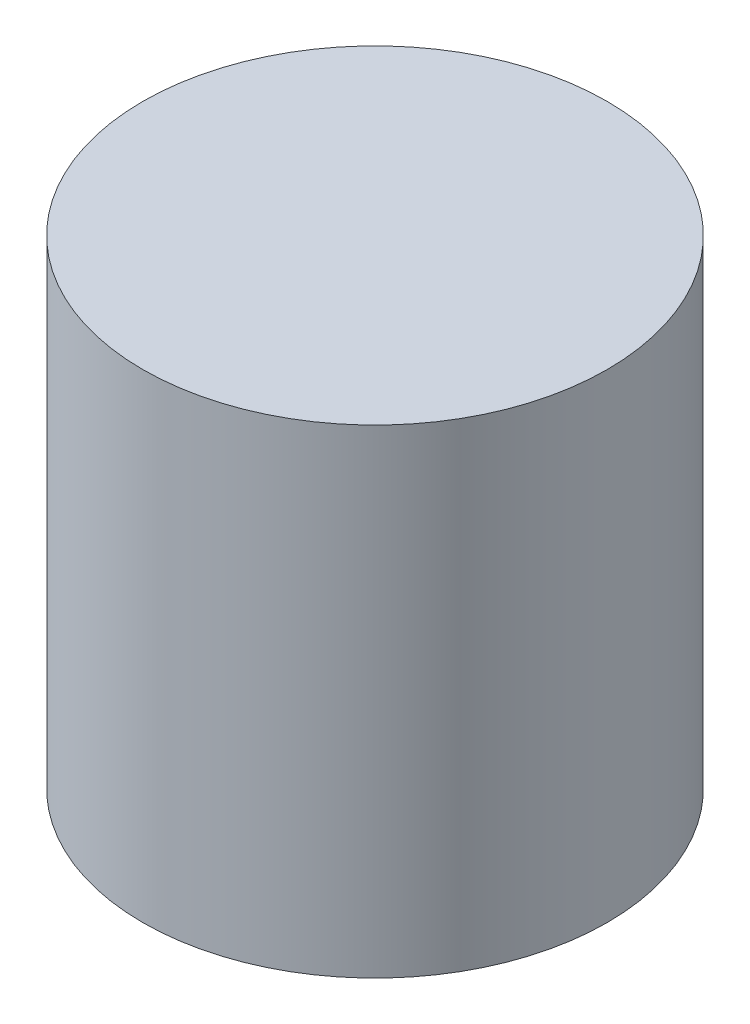
SolidWorks part; units mm, degrees
ref_plane "Front Plane" through (0, 0, 0) normal (0, 0, 1) x (1, 0, 0)
ref_plane "Top Plane" through (0, 0, 0) normal (0, 1, 0) x (1, 0, 0)
ref_plane "Right Plane" through (0, 0, 0) normal (1, 0, 0) x (0, 0, -1)
sketch "Sketch1" plane through (0, 0, 0) normal (0, 1, 0) x (1, 0, 0)
  circle A0 centre (0, 0) radius 8
  dimension "D1" = 16
extrude "Boss-Extrude1" add sketch "Sketch1" along normal blind 16.5
